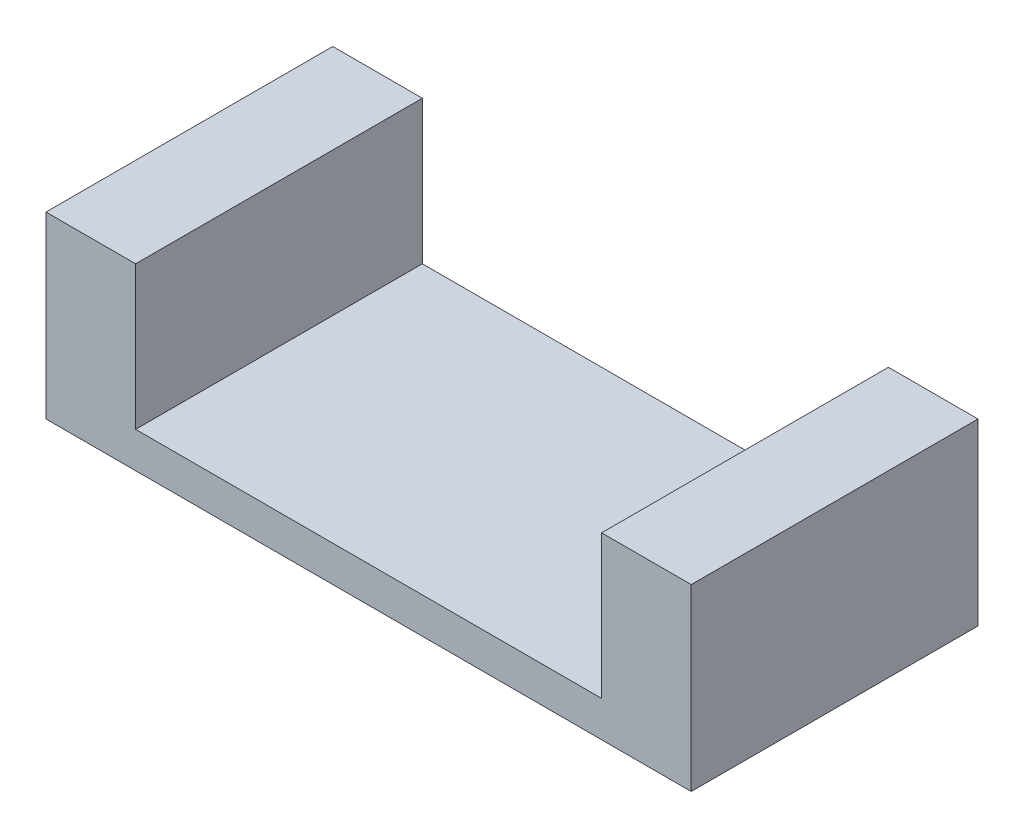
SolidWorks part; units mm, degrees
ref_plane "Front" through (0, 0, 0) normal (0, 0, 1) x (1, 0, 0)
ref_plane "Top" through (0, 0, 0) normal (0, 1, 0) x (1, 0, 0)
ref_plane "Right" through (0, 0, 0) normal (1, 0, 0) x (0, 0, -1)
sketch "Sketch4" plane through (0, 0, 0) normal (0, 0, 1) x (1, 0, 0)
  line L0 (-1.8, 0.5) -> (-1.55, 0.5)
  line L1 (0, 0) -> (-1.8, 0)
  line L2 (0, 0) -> (0, 0.5)
  line L3 (0, 0.5) -> (-0.25, 0.5)
  line L4 (-1.8, 0) -> (-1.8, 0.5)
  line L5 (0, 0) -> (-1.8, 0.5) construction
  line L6 (0, 0.5) -> (-1.8, 0) construction
  line L7 (-1.55, 0.5) -> (-1.55, 0.1)
  line L9 (-0.25, 0.5) -> (-0.25, 0.1)
  line L10 (-0.25, 0.1) -> (-1.55, 0.1)
  point P4 (-0.9, 0.25)
  dimension "D1" = 1.8
  dimension "D2" = 0.5
  dimension "D3" = 0.5
  dimension "D4" = 0.25
  dimension "D5" = 0.25
  dimension "D6" = 0.4
extrude "Boss-Extrude3" add sketch "Sketch4" along normal blind 0.8
